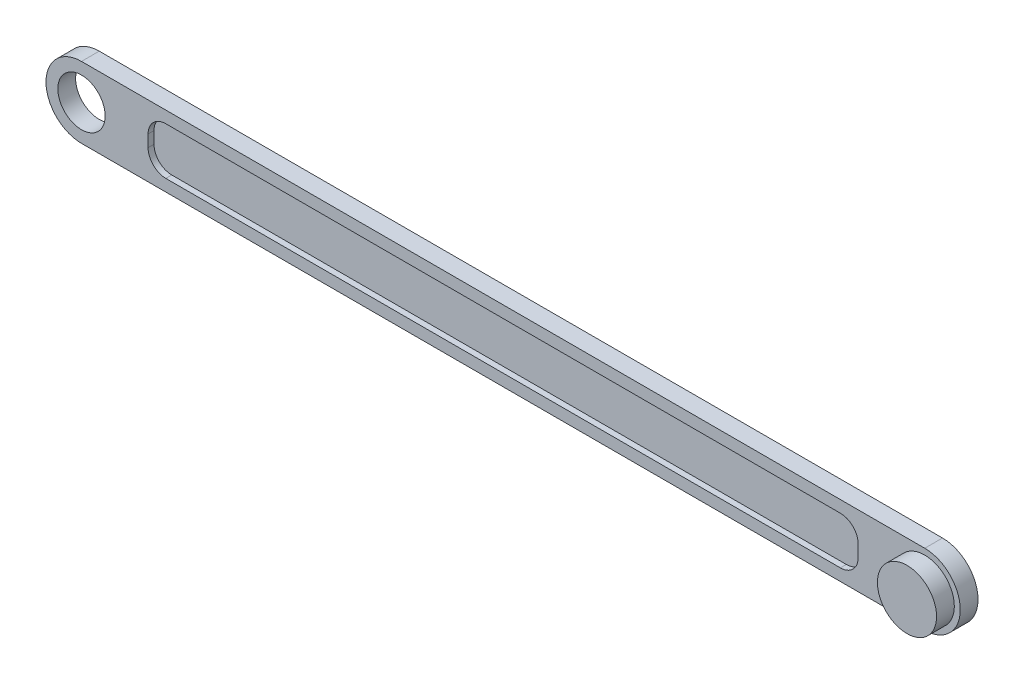
SolidWorks part; units mm, degrees
ref_plane "Front Plane" through (0, 0, 0) normal (0, 0, 1) x (1, 0, 0)
ref_plane "Top Plane" through (0, 0, 0) normal (0, 1, 0) x (1, 0, 0)
ref_plane "Right Plane" through (0, 0, 0) normal (1, 0, 0) x (0, 0, -1)
sketch "Sketch1" plane through (0, 0, 0) normal (0, 0, 1) x (1, 0, 0)
  line L0 (0, 0) -> (142.5, 0) construction
  line L1 (0, 0) -> (142.5, 0) construction
  line L2 (0, 6) -> (142.5, 6)
  line L3 (0, -6) -> (142.5, -6)
  circle A0 centre (0, 0) radius 4
  circle A1 centre (142.5, 0) radius 4
  arc A2 (0, 6) -> (0, -6) centre (0, 0) ccw
  arc A3 (142.5, -6) -> (142.5, 6) centre (142.5, 0) ccw
  point P5 (71.25, 0)
  dimension "D2" = 8
  dimension "D3" = 8
  dimension "D1" = 142.5
  dimension "D4" = 12
extrude "Boss-Extrude1" add sketch "Sketch1" along normal blind 3
sketch "Sketch3" plane through (0, 0, 3) normal (0, 0, 1) x (1, 0, 0)
  circle A0 centre (142.5, 0) radius 4 construction
  circle A1 centre (142.5, 0) radius 4 construction
  circle A2 centre (142.5, 0) radius 5
  dimension "D1" = 10
extrude "Boss-Extrude2" add sketch "Sketch3" along normal blind 3
sketch "Sketch4" plane through (0, 0, 3) normal (0, 0, 1) x (1, 0, 0)
  line L0 (0, 0) -> (142.5, 0) construction
  line L1 (142.5, 6) -> (0, 6) construction
  line L2 (11.25, -4) -> (131.25, -4)
  line L3 (11.25, -4) -> (11.25, 4)
  line L4 (11.25, 4) -> (131.25, 4)
  line L5 (131.25, -4) -> (131.25, 4)
  line L6 (11.25, -4) -> (131.25, 4) construction
  line L7 (11.25, 4) -> (131.25, -4) construction
  point P4 (71.25, 0)
  dimension "D1" = 2
  dimension "D2" = 120
extrude "Cut-Extrude1" cut sketch "Sketch4" against normal blind 1
fillet "Fillet1" radius 3 4 edges at (131.25, -4, 2.5) (131.25, 4, 2.5) (11.25, 4, 2.5) (11.25, -4, 2.5)
